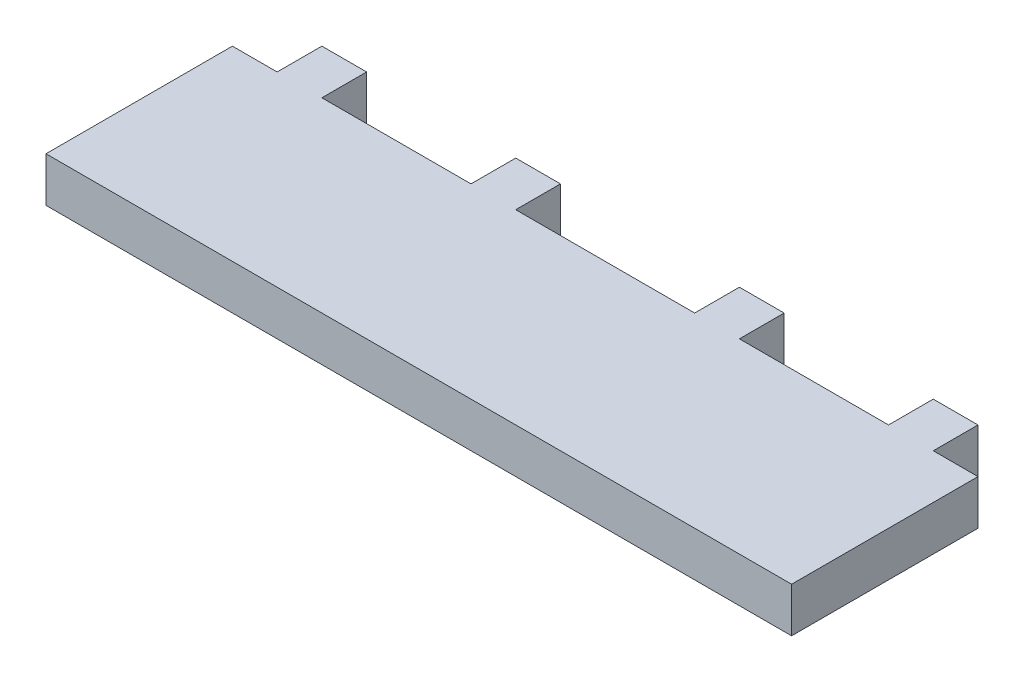
SolidWorks part; units mm, degrees
material "Pine"
ref_plane "정면" through (0, 0, 0) normal (0, 0, 1) x (1, 0, 0)
ref_plane "윗면" through (0, 0, 0) normal (0, 1, 0) x (1, 0, 0)
ref_plane "우측면" through (0, 0, 0) normal (1, 0, 0) x (0, 0, -1)
sketch "Sketch1" plane through (0, 0, 0) normal (0, 0, 1) x (1, 0, 0)
  line L0 (0, -58.8044) -> (0, 63.2041) construction
  line L1 (50, 0) -> (-50, 0)
  line L2 (-50, 0) -> (-50, 6)
  line L3 (-50, 6) -> (50, 6)
  line L4 (50, 0) -> (50, 6)
  point P8 (0, 0)
  point P9 (0, 6)
  dimension "D1" = 50
  dimension "D2" = 6
extrude "Boss-Extrude1" add sketch "Sketch1" along normal blind 25
sketch "Sketch4" plane through (0, 0, 0) normal (0, 0, -1) x (-1, 0, 0)
  line L0 (0, -21.1908) -> (0, 33.4794) construction
  line L1 (-44, 6) -> (-44, 0)
  line L2 (-50, 6) -> (50, 6) construction
  line L3 (50, 0) -> (-50, 0) construction
  line L4 (-44, 0) -> (-38, 0)
  line L5 (-38, 0) -> (-38, 6)
  line L6 (-38, 6) -> (-44, 6)
  line L7 (-50, 0) -> (-50, 6) construction
  line L8 (-18, 6) -> (-18, 0)
  line L9 (-18, 0) -> (-12, 0)
  line L10 (-12, 0) -> (-12, 6)
  line L11 (-12, 6) -> (-18, 6)
  line L12 (12, 6) -> (18, 6)
  line L13 (12, 0) -> (12, 6)
  line L14 (18, 0) -> (12, 0)
  line L15 (18, 6) -> (18, 0)
  line L16 (38, 6) -> (44, 6)
  line L17 (38, 0) -> (38, 6)
  line L18 (44, 0) -> (38, 0)
  line L19 (44, 6) -> (44, 0)
  point P14 (-44, 3)
  dimension "D1" = 6
  dimension "D2" = 6
  dimension "D3" = 6
  dimension "D4" = 20
  dimension "D5" = 6
  dimension "D6" = 100
  dimension "D7" = 6
extrude "Boss-Extrude4" add sketch "Sketch4" along normal blind 6
